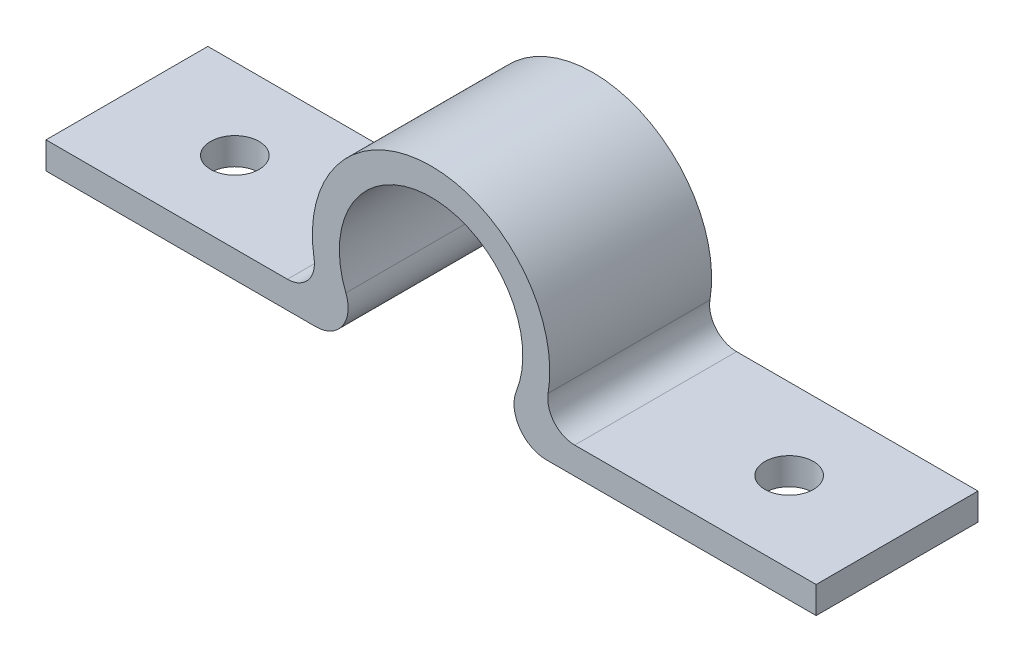
SolidWorks part; units mm, degrees
ref_plane "Front Plane" through (0, 0, 0) normal (0, 0, 1) x (1, 0, 0)
ref_plane "Top Plane" through (0, 0, 0) normal (0, 1, 0) x (1, 0, 0)
ref_plane "Right Plane" through (0, 0, 0) normal (1, 0, 0) x (0, 0, -1)
sketch "Sketch1" plane through (0, 0, 0) normal (0, 0, 1) x (1, 0, 0)
  line L0 (0, 0) -> (50, 0)
  line L1 (92.7468, 0) -> (142.7468, 0)
  line L2 (0, 5) -> (5, 5)
  line L3 (5, 5) -> (51.5282, 5)
  line L4 (0, 5) -> (0, 0)
  line L5 (142.7468, 5) -> (142.7468, 0)
  line L6 (80.2544, 0) -> (142.7468, 0) construction
  line L7 (91.2185, 5) -> (142.7468, 5)
  line L8 (5, 5) -> (5, 5) construction
  line L9 (0, 0) -> (62.4924, 0) construction
  arc A0 (55.5757, 8.2163) -> (87.1711, 8.2163) centre (71.3734, 14.4958) cw
  arc A1 (51.5282, 5) -> (91.2185, 5) centre (71.3734, 14.4958) cw
  arc A2 (62.4924, 0) -> (80.2544, 0) centre (71.3734, 14.4958) cw construction
  arc A3 (87.1711, 8.2163) -> (92.7468, 0) centre (92.7468, 6) ccw
  arc A4 (50, 0) -> (55.5757, 8.2163) centre (50, 6) ccw
  point P3 (74.6813, -8.4879)
  point P7 (0, 0)
  point P14 (62.7055, -3.1905)
  point P15 (63.1, 0)
  point P17 (61.1472, 6.8812)
  point P18 (64.436, 4.0746)
  point P19 (60.8112, 10.398)
  point P20 (0, 0)
  point P21 (58.881, 14.4958)
  point P22 (0, 0)
  point P29 (0, 0)
  point P30 (39.0812, 5)
  point P31 (61.4242, 8.2163)
  dimension "D1" = 17
  dimension "D4" = 6
  dimension "D2" = 31.5954
  dimension "D5" = 50
  dimension "D3" = 5
extrude "Boss-Extrude1" add sketch "Sketch1" along normal blind 30
fillet "Fillet3" radius 5 2 edges at (91.2185, 5, 15) (51.5282, 5, 15)
hole_wizard "M8 Clearance Hole2" positions "Sketch4" profile "Sketch5" hole size "M8" standard "IS" end condition through all
sketch "Sketch4" plane through (0, 5, 0) normal (0, 1, 0) x (1, 0, 0)
  line L0 (0, -30) -> (0, 0) construction
  line L1 (0, 0) -> (44.7503, 0) construction
  line L2 (97.9965, 0) -> (142.7468, 0) construction
  line L3 (142.7468, -30) -> (142.7468, 0) construction
  point P0 (20, -15)
  point P2 (122.7468, -15)
  dimension "D1" = 20
  dimension "D2" = 15
  dimension "D3" = 15
  dimension "D4" = 20
sketch "Sketch5" plane through (20, 5, 15) normal (1, 0, 0) x (0, 0, 1)
  line L0 (0, 0) -> (0, 5)
  line L1 (0, 5) -> (4.5, 5)
  line L2 (4.5, 5) -> (4.5, 0)
  line L5 (4.5, 0) -> (0, 0)
  line L11 (0, -6.35) -> (0, 107.95) construction
  dimension "Thru Hole Dia." = 9
  dimension "Thru Hole Depth" = 5
